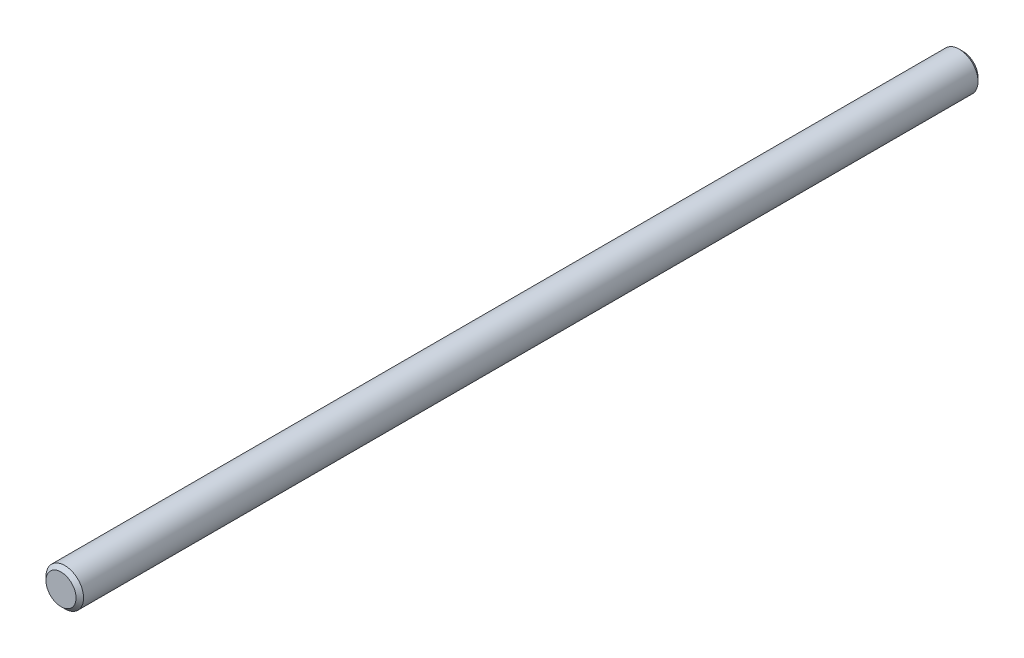
SolidWorks part; units mm, degrees
ref_plane "Front" through (0, 0, 0) normal (0, 0, 1) x (1, 0, 0)
ref_plane "Top" through (0, 0, 0) normal (0, 1, 0) x (1, 0, 0)
ref_plane "Right" through (0, 0, 0) normal (1, 0, 0) x (0, 0, -1)
sketch "Sketch1" plane through (0, 0, 0) normal (0, 0, 1) x (1, 0, 0)
  circle A0 centre (0, 0) radius 1.5875
  dimension "dia" = 3.175
extrude "Extrude1" add sketch "Sketch1" along normal mid plane 76.2
sketch "Sketch2" plane through (0, 0, 0) normal (1, 0, 0) x (0, 0, -1)
  point P0 (-38.1, 1.5875)
  point P1 (38.1, 1.5875)
chamfer "Chamfer1" distance 0.3175 angle 45 2 edges at (1.5875, 0, -38.1) (1.5875, 0, 38.1)
equation "\"D1@Chamfer1\" = \"dia@Sketch1\" * .1"
